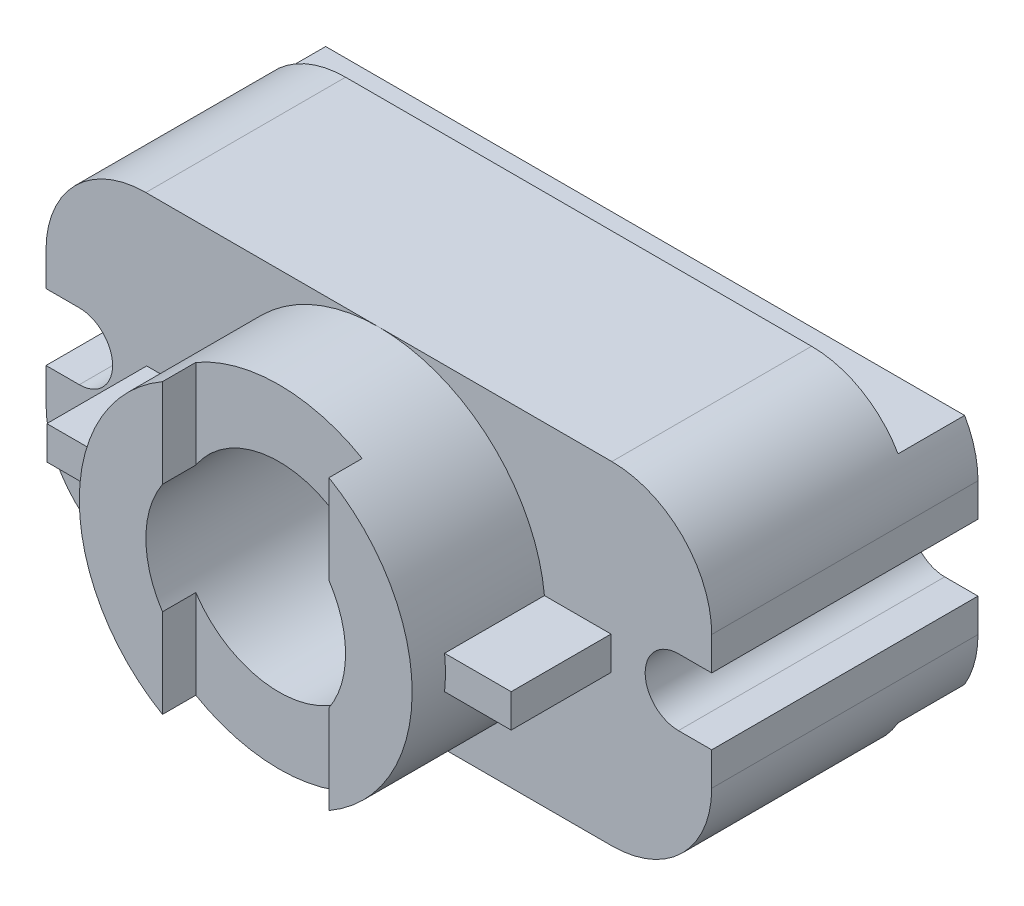
SolidWorks part; units mm, degrees
ref_plane "Front Plane" through (0, 0, 0) normal (0, 0, 1) x (1, 0, 0)
ref_plane "Top Plane" through (0, 0, 0) normal (0, 1, 0) x (1, 0, 0)
ref_plane "Right Plane" through (0, 0, 0) normal (1, 0, 0) x (0, 0, -1)
sketch "Sketch1" plane through (0, 0, 0) normal (0, 0, 1) x (1, 0, 0)
  line L1 (0, 0) -> (200, 0)
  line L2 (0, 0) -> (0, 100)
  line L3 (0, 100) -> (200, 100)
  line L4 (200, 0) -> (200, 100)
  dimension "D1" = 200
  dimension "D2" = 100
extrude "Boss-Extrude1" add sketch "Sketch1" along normal blind 100
sketch "Sketch2" plane through (0, 0, 100) normal (0, 0, 1) x (1, 0, 0)
  line L0 (200, 100) -> (0, 100) construction
  line L1 (0, 0) -> (200, 0) construction
  line L4 (0, 100) -> (200, 100)
  line L5 (0, 100) -> (0, 0)
  line L6 (0, 0) -> (200, 0)
  line L7 (200, 100) -> (200, 0)
  arc A0 (30, 100) -> (0, 70) centre (30, 70) ccw
  arc A1 (30, 0) -> (0, 30) centre (30, 30) cw
  arc A2 (170, 100) -> (200, 70) centre (170, 70) cw
  arc A3 (170, 0) -> (200, 30) centre (170, 30) ccw
  line M1 (0, 100) -> (0, 0)
  line M2 (0, 0) -> (200, 0)
  line M3 (200, 0) -> (200, 100)
  line M4 (200, 100) -> (0, 100)
  dimension "D3" = 30
  dimension "D6" = 30
  dimension "D10" = 30
  dimension "D14" = 30
  dimension "D1" = 30
  dimension "D2" = 30
  dimension "D4" = 70
  dimension "D5" = 30
  dimension "D7" = 30
  dimension "D8" = 70
  dimension "D9" = 30
  dimension "D11" = 30
  dimension "D12" = 70
  dimension "D13" = 30
  dimension "D15" = 70
  dimension "D16" = 30
extrude "Cut-Extrude2" cut sketch "Sketch2" against normal blind 100 contours A0 L4 M1 | A2 L7 M4 | A3 M2 M3 | A1 M2 M1
sketch "Sketch3" plane through (0, 0, 100) normal (0, 0, 1) x (1, 0, 0)
  line L0 (10, 60) -> (0, 60)
  line L1 (0, 70) -> (0, 30) construction
  line L2 (30, 0) -> (170, 0) construction
  line L3 (10, 40) -> (0, 40)
  line L4 (0, 40) -> (0, 60)
  line L5 (190, 60) -> (200, 60)
  line L6 (200, 30) -> (200, 70) construction
  line L7 (200, 60) -> (200, 40)
  line L8 (200, 40) -> (190, 40)
  arc A0 (10, 60) -> (10, 40) centre (10, 50) cw
  arc A1 (190, 60) -> (190, 40) centre (190, 50) ccw
  dimension "D9" = 10
  dimension "D1" = 20
  dimension "D2" = 40
  dimension "D3" = 40
  dimension "D4" = 10
  dimension "D5" = 20
  dimension "D6" = 10
  dimension "D7" = 10
  dimension "D8" = 20
  dimension "D10" = 20
  dimension "D11" = 40
extrude "Cut-Extrude3" cut sketch "Sketch3" against normal blind 100
sketch "Sketch4" plane through (0, 0, 0) normal (1, 0, 0) x (0, 0, -1)
  line L2 (-100, 100) -> (-100, 93)
  line L5 (0, 100) -> (-20, 100)
  line L6 (0, 100) -> (0, 85)
  line L7 (0, 85) -> (-20, 85)
  line L8 (-20, 100) -> (-20, 85)
  line L9 (0, 0) -> (-20, 0)
  line L10 (0, 0) -> (0, 15)
  line L11 (0, 15) -> (-20, 15)
  line L12 (-20, 0) -> (-20, 15)
  dimension "D1" = 20
  dimension "D2" = 20
  dimension "D3" = 15
  dimension "D4" = 15
  dimension "D5" = 7
extrude "Cut-Extrude8" cut sketch "Sketch4" along normal blind 275 contours L5 L8 L7 L6 | L12 L9 L10 L11
sketch "Sketch8" plane through (0, 0, 100) normal (0, 0, 1) x (1, 0, 0)
  line L0 (30, 0) -> (170, 0) construction
  circle A0 centre (100, 50) radius 10
  dimension "D1" = 20
  dimension "D2" = 50
  dimension "D3" = 100
extrude "Cut-Extrude9" cut sketch "Sketch8" against normal blind 275
sketch "Sketch9" plane through (0, 0, 100) normal (0, 0, 1) x (1, 0, 0)
  circle A0 centre (100, 50) radius 10
  circle A1 centre (100, 50) radius 30
  dimension "D1" = 20
  dimension "D2" = 60
extrude "Cut-Extrude10" cut sketch "Sketch9" against normal blind 50
sketch "Sketch10" plane through (0, 0, 100) normal (0, 0, 1) x (1, 0, 0)
  circle A0 centre (100, 50) radius 30
  circle A1 centre (100, 50) radius 50
  dimension "D1" = 60
  dimension "D2" = 100
extrude "Boss-Extrude2" add sketch "Sketch10" along normal blind 20
sketch "Sketch11" plane through (0, 0, 120) normal (0, 0, 1) x (1, 0, 0)
  line L0 (75, 93.3013) -> (75, 66.5831)
  line L1 (125, 93.3013) -> (125, 66.5831)
  line L2 (75, 33.4169) -> (75, 6.6987)
  line L3 (125, 33.4169) -> (125, 6.6987)
  circle A0 centre (100, 50) radius 50 construction
  circle A1 centre (100, 50) radius 30 construction
  arc A2 (100, 100) -> (100, 0) centre (100, 50) ccw construction
  arc A3 (100, 0) -> (100, 100) centre (100, 50) ccw construction
  circle A4 centre (100, 50) radius 30
  circle A5 centre (100, 50) radius 50
  point P12 (50, 50)
  point P16 (150, 50)
  circle M1 centre (100, 50) radius 50
  circle M2 centre (100, 50) radius 30
  dimension "D3" = 60
  dimension "D4" = 100
  dimension "D1" = 25
  dimension "D2" = 25
extrude "Cut-Extrude12" cut sketch "Sketch11" against normal blind 10 contours L1 L0 M1 M2 | L3 L2 M2 M1
sketch "Sketch12" plane through (0, 0, 100) normal (0, 0, 1) x (1, 0, 0)
  line L0 (30, 0) -> (100, 0) construction
  line L1 (50.2506, 55) -> (30.2506, 55)
  line L2 (50.2506, 55) -> (50.2506, 45)
  line L3 (50.2506, 45) -> (30.2506, 45)
  line L4 (30.2506, 55) -> (30.2506, 45)
  arc A0 (100, 100) -> (100, 0) centre (100, 50) ccw construction
  dimension "D1" = 10
  dimension "D2" = 45
  dimension "D3" = 20
extrude "Boss-Extrude3" add sketch "Sketch12" along normal blind 10
sketch "Sketch13" plane through (0, 0, 100) normal (0, 0, 1) x (1, 0, 0)
  line L0 (100, 0) -> (170, 0) construction
  line L1 (149.7494, 55) -> (169.7494, 55)
  line L2 (149.7494, 55) -> (149.7494, 45)
  line L3 (149.7494, 45) -> (169.7494, 45)
  line L4 (169.7494, 55) -> (169.7494, 45)
  arc A0 (100, 0) -> (100, 100) centre (100, 50) ccw construction
  point P7 (135, 0)
  dimension "D1" = 10
  dimension "D2" = 45
  dimension "D3" = 20
extrude "Boss-Extrude4" add sketch "Sketch13" along normal blind 10
sketch "Sketch14" plane through (0, 0, 100) normal (0, 0, 1) x (1, 0, 0)
  line L0 (0, 70) -> (0, 60)
  line L1 (30, 100) -> (170, 100)
  line L2 (30, 100) -> (30, 0)
  line L3 (30, 0) -> (170, 0)
  line L4 (170, 100) -> (170, 0)
  line L5 (0, 60) -> (10, 60)
  line L6 (10, 40) -> (0, 40)
  line L7 (0, 40) -> (0, 30)
  line L8 (200, 70) -> (200, 60)
  line L9 (200, 60) -> (190, 60)
  line L10 (190, 40) -> (200, 40)
  line L11 (200, 40) -> (200, 30)
  arc A0 (30, 100) -> (0, 70) centre (30, 70) ccw
  arc A1 (30, 100) -> (0, 70) centre (30, 70) ccw construction
  arc A2 (10, 60) -> (10, 40) centre (10, 50) cw
  arc A3 (10, 40) -> (10, 60) centre (10, 50) ccw construction
  arc A4 (0, 30) -> (30, 0) centre (30, 30) ccw
  arc A5 (170, 100) -> (200, 70) centre (170, 70) cw
  arc A6 (200, 70) -> (170, 100) centre (170, 70) ccw construction
  arc A7 (190, 60) -> (190, 40) centre (190, 50) ccw
  arc A8 (200, 30) -> (170, 0) centre (170, 30) cw
  line M1 (30.2506, 55) -> (50.2506, 55)
  arc M2 (50.2506, 55) -> (100, 100) centre (100, 50) cw
  line M3 (100, 100) -> (30, 100)
  arc M4 (30, 100) -> (0, 70) centre (30, 70) ccw
  line M5 (0, 70) -> (0, 60)
  line M6 (0, 60) -> (10, 60)
  arc M7 (10, 60) -> (10, 40) centre (10, 50) cw
  line M8 (10, 40) -> (0, 40)
  line M9 (0, 40) -> (0, 30)
  arc M10 (0, 30) -> (30, 0) centre (30, 30) ccw
  line M11 (30, 0) -> (100, 0)
  arc M12 (100, 0) -> (50.2506, 45) centre (100, 50) cw
  line M13 (50.2506, 45) -> (30.2506, 45)
  line M14 (30.2506, 45) -> (30.2506, 55)
extrude "Cut-Extrude13" cut sketch "Sketch14" against normal blind 20 contours A8 L11 L10 A7 L9 L8 A5 L4 | L4 L1 L3 M2 M1 M14 M13 M12 | L2 M3 M11 M12 M13 M14 M1 M2 | L2 M4 M5 M6 M7 M8 M9 M10
sketch "Sketch15" plane through (0, 0, 100) normal (0, 0, -1) x (-1, 0, 0)
  circle A0 centre (-100, 50) radius 30
  circle A1 centre (-100, 50) radius 50
  dimension "D1" = 60
  dimension "D2" = 100
extrude "Boss-Extrude5" add sketch "Sketch15" along normal blind 20
sketch "Sketch16" plane through (0, 0, 110) normal (0, 0, 1) x (1, 0, 0)
  line L1 (30.2506, 55) -> (50.2506, 55)
  line L2 (30.2506, 55) -> (30.2506, 45)
  line L3 (30.2506, 45) -> (50.2506, 45)
  line L4 (50.2506, 55) -> (50.2506, 45)
  line L5 (169.7494, 55) -> (149.7494, 55)
  line L6 (169.7494, 55) -> (169.7494, 45)
  line L7 (169.7494, 45) -> (149.7494, 45)
  line L8 (149.7494, 55) -> (149.7494, 45)
extrude "Boss-Extrude6" add sketch "Sketch16" against normal blind 30
